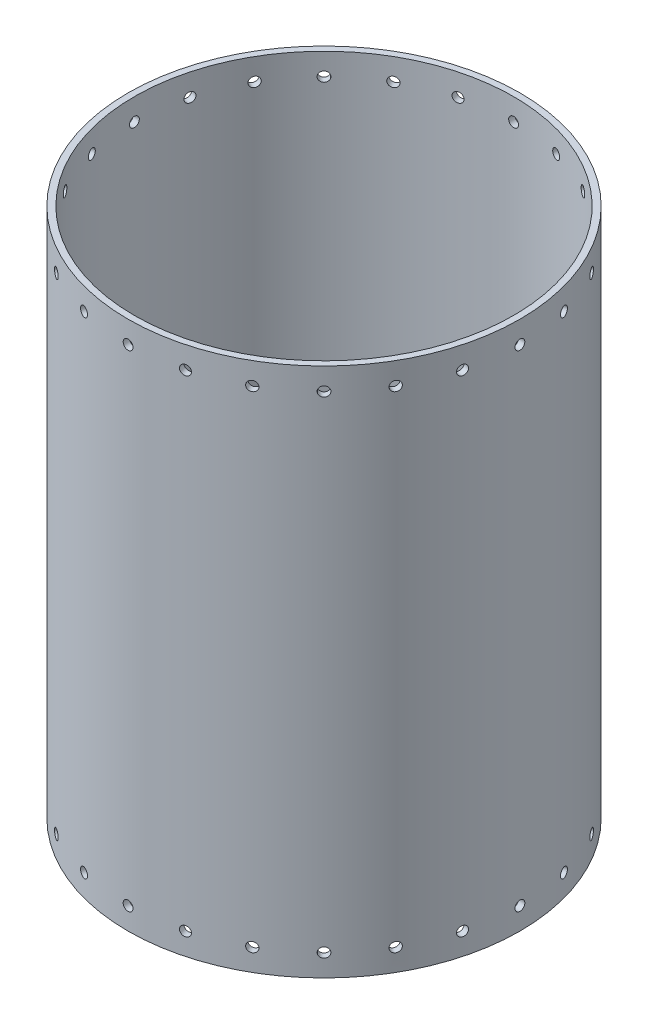
SolidWorks part; units mm, degrees
material "6061-T6 (SS)"
ref_plane "Front Plane" through (0, 0, 0) normal (0, 0, 1) x (1, 0, 0)
ref_plane "Top Plane" through (0, 0, 0) normal (0, 1, 0) x (1, 0, 0)
ref_plane "Right Plane" through (0, 0, 0) normal (1, 0, 0) x (0, 0, -1)
sketch "Sketch1" plane through (0, 0, 0) normal (0, 1, 0) x (1, 0, 0)
  circle A0 centre (0, 0) radius 98.425
  dimension "D1" = 196.85
extrude "Extrude-Thin1" add sketch "Sketch1" along normal blind 275.082 thin
ref_plane "Plane1" through (0, 263.652, 0) normal (0, 1, 0) x (1, 0, 0)
sketch "Sketch2" plane through (0, 263.652, 0) normal (0, 1, 0) x (1, 0, 0)
  line L0 (0, 0) -> (0, -116.6708) construction
  line L2 (0, -93.98) -> (2.54, -93.98)
  line L3 (0, -93.98) -> (0, -106.68)
  line L4 (0, -106.68) -> (2.54, -106.68)
  line L5 (2.54, -93.98) -> (2.54, -106.68)
  point P7 (-2.54, -93.98)
  dimension "D1" = 12.7
  dimension "D2" = 5.08
  dimension "D3" = 2.54
  dimension "D4" = 93.98
revolve "Cut-Revolve1" cut sketch "Sketch2" angle 360 about L0
sketch "Sketch3" plane through (0, 0, 0) normal (0, 0, 1) x (1, 0, 0)
  line L0 (0, 0) -> (0, 275.082) construction
  line L1 (98.425, 275.082) -> (-98.425, 275.082) construction
pattern_circular "CirPattern1" count 24 over 360 about axis through (0, 0, 0) along (0, 1, 0) of "Cut-Revolve1"
ref_plane "Plane2" through (0, 137.541, 0) normal (0, 1, 0) x (1, 0, 0)
mirror "Mirror1" about plane through (0, 137.541, 0) normal (0, 1, 0) of "CirPattern1", "Cut-Revolve1"
